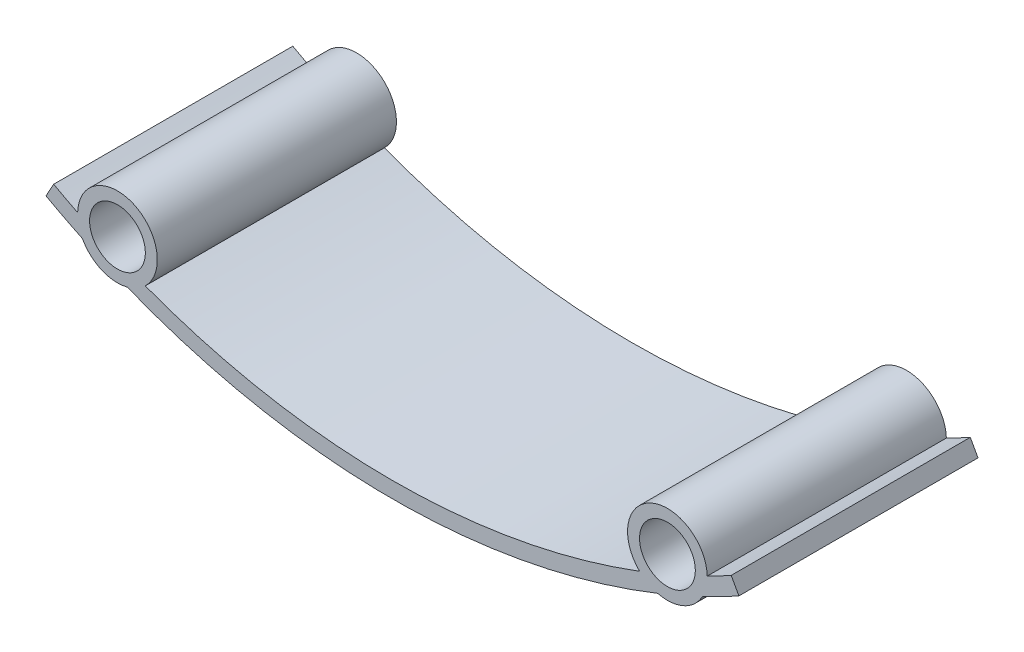
SolidWorks part; units mm, degrees
ref_plane "Front Plane" through (0, 0, 0) normal (0, 0, 1) x (1, 0, 0)
ref_plane "Top Plane" through (0, 0, 0) normal (0, 1, 0) x (1, 0, 0)
ref_plane "Right Plane" through (0, 0, 0) normal (1, 0, 0) x (0, 0, -1)
sketch "Sketch1" plane through (0, 0, 0) normal (0, 0, 1) x (1, 0, 0)
  line L0 (0, 90) -> (0, 0) construction
  line L1 (-43.4659, 11.1919) -> (-42.5, 12.9432)
  line L2 (0, 90) -> (-42.5, 12.9432) construction
  line L6 (42.5, 12.9432) -> (0, 90) construction
  line L7 (-42.5, 12.9432) -> (42.5, 12.9432) construction
  line L8 (-34.5, 11.2234) -> (34.5, 11.2234) construction
  line L9 (42.5, 12.9432) -> (43.4659, 11.1919)
  arc A0 (38.8945, 8.8383) -> (-38.8945, 8.8383) centre (0, 90) ccw construction
  arc A2 (42.5, 12.9432) -> (39.4981, 11.3622) centre (0, 90) cw
  circle A3 centre (-34.5, 11.2234) radius 3.5
  circle A5 centre (34.5, 11.2234) radius 3.5
  arc A10 (-43.4659, 11.1919) -> (-38.8945, 8.8383) centre (0, 90) ccw construction
  circle A11 centre (0, 90) radius 86 construction
  arc A12 (-31.0086, 7.6443) -> (-39.4981, 11.3622) centre (-34.5, 11.2234) ccw
  arc A13 (39.4981, 11.3622) -> (31.0086, 7.6443) centre (34.5, 11.2234) ccw
  arc A14 (-33.2729, 6.3763) -> (33.2729, 6.3763) centre (0, 90) ccw construction
  arc A15 (-38.8945, 8.8383) -> (-43.4659, 11.1919) centre (0, 90) cw
  arc A16 (-33.2729, 6.3763) -> (33.2729, 6.3763) centre (0, 90) ccw construction
  arc A17 (-39.4981, 11.3622) -> (-42.5, 12.9432) centre (0, 90) cw
  arc A18 (-38.8945, 8.8383) -> (-33.2729, 6.3763) centre (-34.5, 11.2234) ccw
  arc A19 (33.2729, 6.3763) -> (-33.2729, 6.3763) centre (0, 90) cw
  arc A20 (38.8945, 8.8383) -> (43.4659, 11.1919) centre (0, 90) ccw construction
  arc A21 (31.0086, 7.6443) -> (-31.0086, 7.6443) centre (0, 90) cw
  circle A23 centre (-34.5, 11.2234) radius 5 construction
  circle A24 centre (34.5, 11.2234) radius 5 construction
  arc A25 (33.2729, 6.3763) -> (38.8945, 8.8383) centre (34.5, 11.2234) ccw
  arc A26 (38.8945, 8.8383) -> (-40.3252, 9.5396) centre (0, 90) ccw construction
  arc A27 (38.8945, 8.8383) -> (43.4659, 11.1919) centre (0, 90) ccw
  point P14 (0, 11.2234)
  dimension "D1" = 85
  dimension "D3" = 5
  dimension "D4" = 2
  dimension "D6" = 7
  dimension "D7" = 10
  dimension "D5" = 172
  dimension "D8" = 90
  dimension "D2" = 69
extrude "Boss-Extrude1" add sketch "Sketch1" along normal blind 30 contours A25 A27 L9 A2 A13 A21 A12 A17 L1 A15 A18 A19 A3 A5
